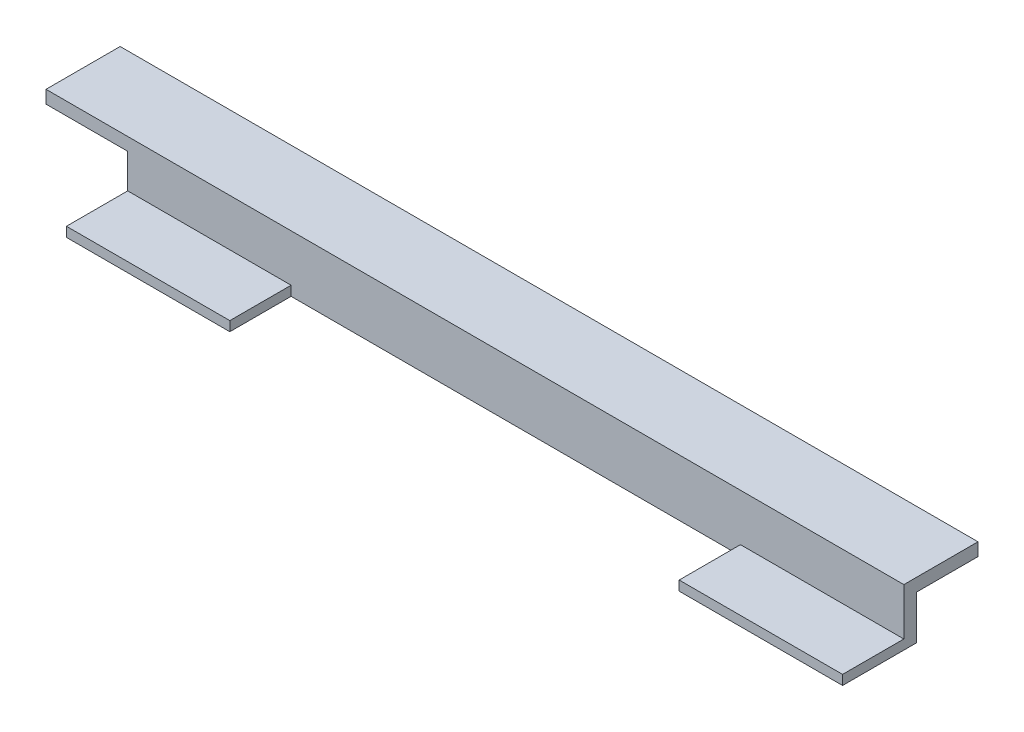
SolidWorks part; units mm, degrees
ref_plane "Front Plane" through (0, 0, 0) normal (0, 0, 1) x (1, 0, 0)
ref_plane "Top Plane" through (0, 0, 0) normal (0, 1, 0) x (1, 0, 0)
ref_plane "Right Plane" through (0, 0, 0) normal (1, 0, 0) x (0, 0, -1)
sketch "Sketch1" plane through (0, 0, 0) normal (1, 0, 0) x (0, 0, -1)
  line L3 (-2, 0) -> (-2, 8.826)
  line L4 (-2, 8.826) -> (9.525, 8.826)
  line L5 (9.525, 8.826) -> (9.525, 6.826)
  line L6 (9.525, 6.826) -> (0, 6.826)
  line L7 (0, 6.826) -> (0, 0)
  line L8 (0, 0) -> (-2, 0)
  line L9 (0, 0) -> (9.525, 0)
  line L10 (9.525, 0) -> (9.525, 1.5)
  line L11 (9.525, 1.5) -> (-2, 1.5)
  line L13 (-2, 1.5) -> (-11.525, 1.5)
  line L14 (-2, 1.5) -> (-2, 0)
  line L15 (-2, 0) -> (-11.525, 0)
  line L16 (-11.525, 1.5) -> (-11.525, 0)
  point P12 (-2, 0)
  point P13 (-6.4295, 0)
  dimension "D1" = 6.826
  dimension "D2" = 2
  dimension "D3" = 2
  dimension "D4" = 9.525
  dimension "D5" = 1.5
extrude "Boss-Extrude1" add sketch "Sketch1" along normal blind 120.65 contours L11 L7 L6 L5 L4 L3 | L7 L11 L3 L8 | L13 L16 L15 L3
sketch "Sketch2" plane through (0, 0, 0) normal (0, -1, 0) x (1, 0, 0)
  line L10 (120.65, 2) -> (0, 2) construction
  line L11 (25.4, 2) -> (95.25, 2)
  line L13 (25.4, 2) -> (25.4, 11.525)
  line L14 (25.4, 11.525) -> (95.25, 11.525)
  line L15 (95.25, 2) -> (95.25, 11.525)
  line L16 (120.65, 11.525) -> (0, 11.525) construction
  line L17 (120.65, -9.525) -> (0, -9.525) construction
  line L18 (0, 2) -> (0, 11.525) construction
  point P8 (60.325, 2)
  point P11 (60.325, -9.525)
  dimension "D1" = 25.4
extrude "Cut-Extrude1" cut sketch "Sketch2" against normal through all
sketch "Sketch3" plane through (0, 0, 0) normal (-1, 0, 0) x (0, 0, 1)
  line L1 (-9.525, 6.826) -> (2, 6.826)
  line L2 (-9.525, 6.826) -> (-9.525, 8.826)
  line L3 (-9.525, 8.826) -> (2, 8.826)
  line L4 (2, 6.826) -> (2, 8.826)
extrude "Boss-Extrude3" add sketch "Sketch3" along normal blind 12.7
